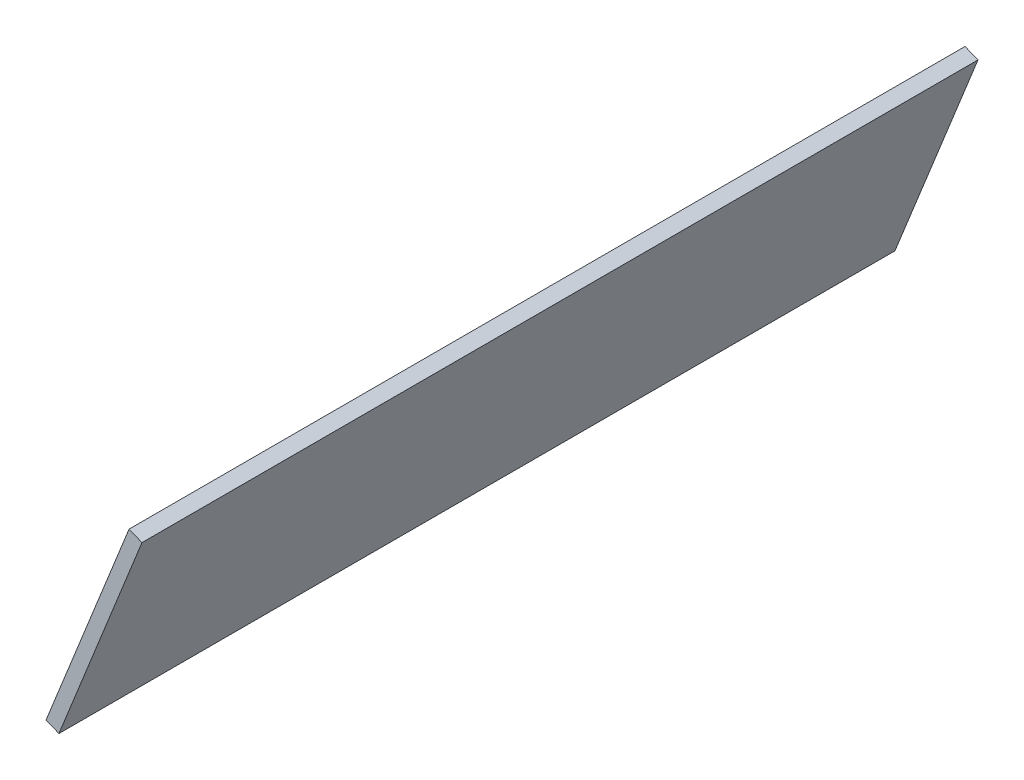
SolidWorks part; units mm, degrees
ref_plane "Plan de face" through (0, 0, 0) normal (0, 0, 1) x (1, 0, 0)
ref_plane "Plan de dessus" through (0, 0, 0) normal (0, 1, 0) x (1, 0, 0)
ref_plane "Plan de droite" through (0, 0, 0) normal (1, 0, 0) x (0, 0, -1)
sketch "Esquisse1" plane through (0, 0, 0) normal (0, 0, 1) x (1, 0, 0)
  line L0 (-71.0842, 377.6794) -> (-130.6859, 229.2028)
  line L1 (-130.6859, 229.2028) -> (-121.4057, 225.4775)
  line L2 (-121.4057, 225.4775) -> (-61.804, 373.9541)
  line L3 (-61.804, 373.9541) -> (-71.0842, 377.6794)
  dimension "D1" = 10
extrude "Boss.-Extru.1" add sketch "Esquisse1" along normal blind 600
